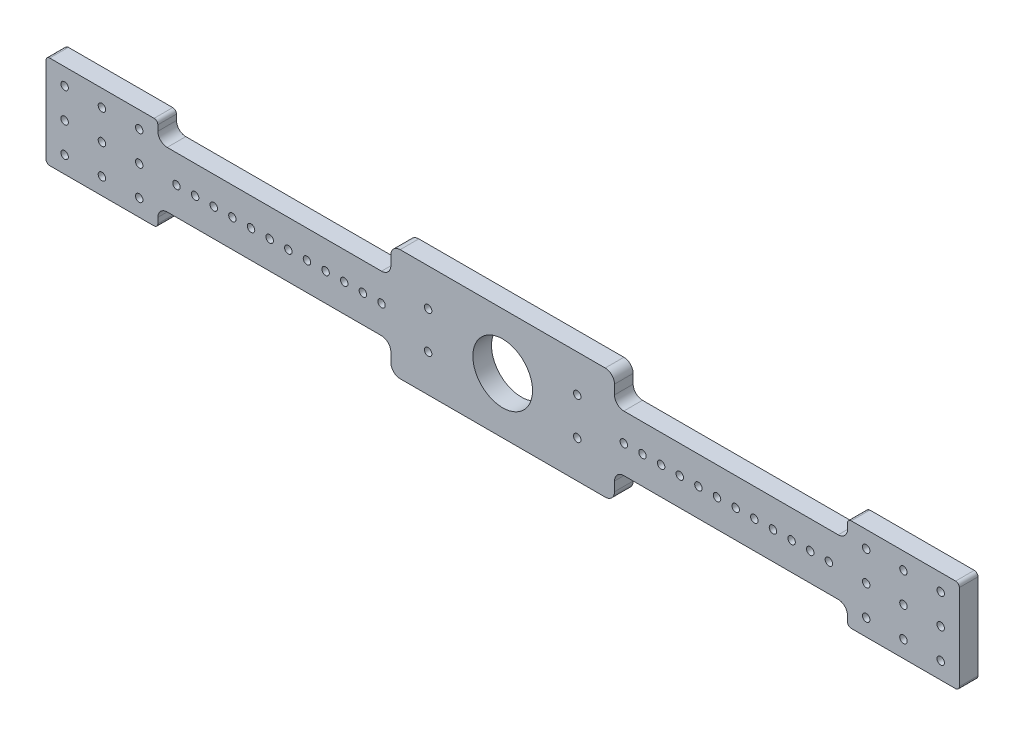
SolidWorks part; units mm, degrees
material "1060 Alloy"
ref_plane "Front Plane" through (0, 0, 0) normal (0, 0, 1) x (1, 0, 0)
ref_plane "Top Plane" through (0, 0, 0) normal (0, 1, 0) x (1, 0, 0)
ref_plane "Right Plane" through (0, 0, 0) normal (1, 0, 0) x (0, 0, -1)
sketch "Sketch1" plane through (0, 0, 0) normal (0, 0, 1) x (1, 0, 0)
  line L0 (245, 5) -> (245, 55)
  line L1 (-60, 0) -> (60, 0)
  line L2 (185, 55) -> (245, 55)
  line L3 (185, 45) -> (185, 55)
  line L4 (60, 0) -> (60, 15)
  line L5 (60, 45) -> (185, 45)
  line L6 (60, 60) -> (60, 45)
  line L7 (60, 15) -> (185, 15)
  line L8 (245, 30) -> (0, 30) construction
  line L9 (-60, 60) -> (60, 60)
  line L10 (0, 0) -> (0, 60) construction
  line L11 (185, 5) -> (245, 5)
  line L12 (-60, 60) -> (-60, 45)
  line L13 (215, 30) -> (215, 5) construction
  line L14 (185, 15) -> (185, 5)
  line L15 (-60, 45) -> (-185, 45)
  line L16 (-185, 45) -> (-185, 55)
  line L17 (-185, 55) -> (-245, 55)
  line L18 (-245, 5) -> (-245, 55)
  line L19 (-185, 5) -> (-245, 5)
  line L20 (-185, 15) -> (-185, 5)
  line L21 (-60, 15) -> (-185, 15)
  line L22 (-60, 0) -> (-60, 15)
  dimension "D1" = 245
  dimension "D2" = 60
  dimension "D3" = 60
  dimension "D4" = 30
  dimension "D5" = 25
  dimension "D6" = 15
extrude "Boss-Extrude1" add sketch "Sketch1" along normal blind 10
sketch "Sketch2" plane through (0, 0, 10) normal (0, 0, 1) x (1, 0, 0)
  line L0 (0, 0) -> (0, 60) construction
  line L1 (-60, 0) -> (60, 0) construction
  line L2 (60, 60) -> (-60, 60) construction
  line L3 (0, 30) -> (245, 30) construction
  line L4 (245, 5) -> (245, 55) construction
  circle A0 centre (40, 20) radius 2
  circle A2 centre (40, 40) radius 2
  circle A3 centre (-40, 40) radius 2
  circle A4 centre (-40, 20) radius 2
  circle A5 centre (0, 30) radius 16
  dimension "D3" = 4
  dimension "D6" = 32
  dimension "D1" = 40
  dimension "D2" = 10
extrude "Cut-Extrude1" cut sketch "Sketch2" against normal through all
fillet "Fillet1" radius 5 12 edges at (-185, 45, 5) (-185, 15, 5) (185, 15, 5) (185, 45, 5) (-60, 45, 5) (-60, 60, 5) (-60, 15, 5) (-60, 0, 5) (60, 45, 5) (60, 60, 5) (60, 15, 5) (60, 0, 5)
sketch "Sketch3" plane through (0, 0, 10) normal (0, 0, 1) x (1, 0, 0)
  line L0 (-245, 30) -> (245, 30) construction
  line L1 (-245, 55) -> (-245, 5) construction
  line L2 (245, 5) -> (245, 55) construction
  line L3 (0, 30) -> (0, 60) construction
  line L4 (55, 60) -> (-55, 60) construction
  circle A0 centre (-125, 30) radius 2
  circle A1 centre (125, 30) radius 2
  dimension "D2" = 4
  dimension "D1" = 125
extrude "Cut-Extrude2" cut sketch "Sketch3" against normal through all
sketch "Sketch4" plane through (0, 0, 10) normal (0, 0, 1) x (1, 0, 0)
  line L0 (0, 60) -> (0, 0) construction
  line L1 (55, 60) -> (-55, 60) construction
  line L2 (-55, 0) -> (55, 0) construction
  line L3 (-245, 30) -> (245, 30) construction
  line L4 (-245, 55) -> (-245, 5) construction
  line L5 (245, 5) -> (245, 55) construction
  line L6 (-235, 14) -> (-195, 14) construction
  line L7 (235, 14) -> (195, 14) construction
  circle A0 centre (-235, 14) radius 2
  circle A1 centre (-215, 14) radius 2
  circle A2 centre (-195, 14) radius 2
  circle A3 centre (-195, 46) radius 2
  circle A4 centre (-215, 46) radius 2
  circle A5 centre (-235, 46) radius 2
  circle A6 centre (235, 46) radius 2
  circle A7 centre (215, 46) radius 2
  circle A8 centre (195, 46) radius 2
  circle A9 centre (195, 14) radius 2
  circle A10 centre (215, 14) radius 2
  circle A11 centre (235, 14) radius 2
  circle A12 centre (-235, 30) radius 2
  circle A13 centre (-215, 30) radius 2
  circle A14 centre (-195, 30) radius 2
  circle A15 centre (215, 30) radius 2
  circle A16 centre (235, 30) radius 2
  circle A17 centre (195, 30) radius 2
  dimension "D3" = 4
  dimension "D1" = 40
  dimension "D2" = 10
  dimension "D4" = 16
extrude "Cut-Extrude3" cut sketch "Sketch4" against normal through all
pattern_linear "LPattern1" count 6 spacing 10 along (-1, 0, 0) count 6 spacing 10 along (1, 0, 0) of "Cut-Extrude2"
sketch "Sketch5" plane through (0, 0, 10) normal (0, 0, 1) x (1, 0, 0)
  line L0 (-73, 30) -> (73, 30) construction
  line L1 (0, 0) -> (0, 60) construction
  line L2 (-55, 0) -> (55, 0) construction
  line L3 (55, 60) -> (-55, 60) construction
  circle A0 centre (-75, 30) radius 2 construction
  circle A1 centre (75, 30) radius 2 construction
  circle A2 centre (-65, 30) radius 2
  circle A3 centre (65, 30) radius 2
  dimension "D1" = 10
extrude "Cut-Extrude4" cut sketch "Sketch5" against normal through all
fillet "Fillet2" radius 2 8 edges at (185, 5, 5) (245, 5, 5) (245, 55, 5) (185, 55, 5) (-185, 55, 5) (-185, 5, 5) (-245, 55, 5) (-245, 5, 5)
